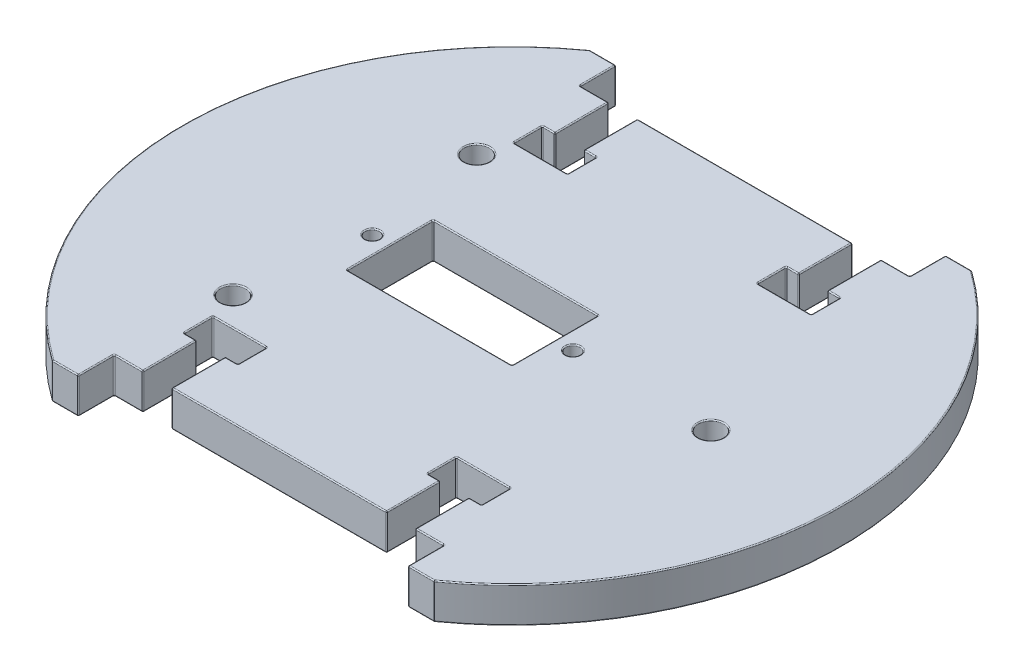
SolidWorks part; units mm, degrees
ref_plane "Front Plane" through (0, 0, 0) normal (0, 0, 1) x (1, 0, 0)
ref_plane "Top Plane" through (0, 0, 0) normal (0, 1, 0) x (1, 0, 0)
ref_plane "Right Plane" through (0, 0, 0) normal (1, 0, 0) x (0, 0, -1)
sketch "Sketch1" plane through (0, 0, 0) normal (0, 1, 0) x (1, 0, 0)
  line L0 (-26.6411, 37.5) -> (-23, 37.5)
  line L1 (0, 0) -> (-46, 0) construction
  line L3 (-23, 37.5) -> (-23, 32.5)
  line L4 (-23, 32.5) -> (23, 32.5)
  line L5 (23, 37.5) -> (23, 32.5)
  line L6 (23, 37.5) -> (26.6411, 37.5)
  line L7 (-26.6411, -37.5) -> (-23, -37.5)
  line L8 (-23, -37.5) -> (-23, -32.5)
  line L9 (-23, -32.5) -> (23, -32.5)
  line L10 (23, -37.5) -> (23, -32.5)
  line L11 (23, -37.5) -> (26.6411, -37.5)
  line L12 (27.75, 0) -> (-21.93, 0) construction
  line L13 (-17, -6) -> (6, -6)
  line L14 (-17, -6) -> (-17, 6)
  line L15 (-17, 6) -> (6, 6)
  line L16 (6, -6) -> (6, 6)
  line L17 (-17, -6) -> (6, 6) construction
  line L18 (-17, 6) -> (6, -6) construction
  line L19 (-21.93, 17) -> (-21.93, -17) construction
  arc A0 (-26.6411, 37.5) -> (-26.6411, -37.5) centre (0, 0) ccw
  arc A1 (26.6411, -37.5) -> (26.6411, 37.5) centre (0, 0) ccw
  circle A2 centre (-19.5, 0) radius 1
  circle A3 centre (8.5, 0) radius 1
  circle A4 centre (-21.93, 17) radius 1.75
  circle A5 centre (-21.93, -17) radius 1.75
  circle A6 centre (27.75, 0) radius 1.75
  point P9 (0, 32.5)
  point P16 (-5.5, 0)
  dimension "D1" = 92
  dimension "D8" = 2
  dimension "D9" = 2
  dimension "D15" = 3.5
  dimension "D2" = 37.5
  dimension "D3" = 46
  dimension "D4" = 5
  dimension "D5" = 6
  dimension "D6" = 23
  dimension "D7" = 12
  dimension "D10" = 2.5
  dimension "D11" = 2.5
  dimension "D12" = 34
  dimension "D13" = 27.75
  dimension "D14" = 49.68
extrude "Boss-Extrude1" add sketch "Sketch1" along normal blind 5
sketch "Sketch2" plane through (0, 5, 0) normal (0, 1, 0) x (1, 0, 0)
  line L0 (23, 32.5) -> (-23, 32.5) construction
  line L1 (-19, 25) -> (-15, 25)
  line L2 (-19, 25) -> (-19, 32.5)
  line L3 (-19, 32.5) -> (-15, 32.5)
  line L4 (-15, 25) -> (-15, 32.5)
  line L5 (-19, 25) -> (-15, 32.5) construction
  line L6 (-19, 32.5) -> (-15, 25) construction
  line L7 (-23, 32.5) -> (-23, 37.5) construction
  line L8 (-20.75, 21) -> (-13.25, 21)
  line L9 (-20.75, 21) -> (-20.75, 25)
  line L10 (-20.75, 25) -> (-13.25, 25)
  line L11 (-13.25, 21) -> (-13.25, 25)
  line L12 (-20.75, 21) -> (-13.25, 25) construction
  line L13 (-20.75, 25) -> (-13.25, 21) construction
  line L14 (-17, 0) -> (0, 0) construction
  line L15 (-17, 6) -> (-17, -6) construction
  line L16 (0, 0) -> (0, 32.5) construction
  line L17 (20.75, 25) -> (13.25, 21) construction
  line L18 (20.75, 21) -> (13.25, 25) construction
  line L19 (19, 32.5) -> (15, 25) construction
  line L20 (19, 25) -> (15, 32.5) construction
  line L21 (13.25, 21) -> (13.25, 25)
  line L22 (20.75, 25) -> (13.25, 25)
  line L23 (20.75, 21) -> (20.75, 25)
  line L24 (20.75, 21) -> (13.25, 21)
  line L25 (15, 25) -> (15, 32.5)
  line L26 (19, 32.5) -> (15, 32.5)
  line L27 (19, 25) -> (19, 32.5)
  line L28 (19, 25) -> (15, 25)
  line L29 (19, -25) -> (15, -32.5) construction
  line L30 (19, -32.5) -> (15, -25) construction
  line L31 (20.75, -21) -> (13.25, -25) construction
  line L32 (20.75, -25) -> (13.25, -21) construction
  line L33 (-20.75, -25) -> (-13.25, -21) construction
  line L34 (-20.75, -21) -> (-13.25, -25) construction
  line L35 (-19, -32.5) -> (-15, -25) construction
  line L36 (-19, -25) -> (-15, -32.5) construction
  line L37 (19, -25) -> (15, -25)
  line L38 (19, -25) -> (19, -32.5)
  line L39 (19, -32.5) -> (15, -32.5)
  line L40 (15, -25) -> (15, -32.5)
  line L41 (20.75, -21) -> (13.25, -21)
  line L42 (20.75, -21) -> (20.75, -25)
  line L43 (20.75, -25) -> (13.25, -25)
  line L44 (13.25, -21) -> (13.25, -25)
  line L45 (-13.25, -21) -> (-13.25, -25)
  line L46 (-20.75, -25) -> (-13.25, -25)
  line L47 (-20.75, -21) -> (-20.75, -25)
  line L48 (-20.75, -21) -> (-13.25, -21)
  line L49 (-15, -25) -> (-15, -32.5)
  line L50 (-19, -32.5) -> (-15, -32.5)
  line L51 (-19, -25) -> (-19, -32.5)
  line L52 (-19, -25) -> (-15, -25)
  point P0 (-17, 28.75)
  point P7 (-17, 23)
  point P28 (17, 23)
  point P29 (17, 28.75)
  point P46 (17, -28.75)
  point P47 (17, -23)
  point P48 (-17, -23)
  point P49 (-17, -28.75)
  dimension "D1" = 4
  dimension "D2" = 4
  dimension "D3" = 7.5
  dimension "D4" = 4
  dimension "D5" = 7.5
extrude "Cut-Extrude1" cut sketch "Sketch2" against normal through all contours L2 L3 L4 L1 | L9 L10 L11 L8 | L25 L26 L27 L28 | L21 L22 L23 L24 | L40 L39 L38 L37 | L44 L43 L42 L41 | L45 L46 L47 L48 | L49 L50 L51 L52
fillet "Fillet1" radius 0.15 123 edges at (-19, 2.5, -25) (-19, 2.5, -32.5) (-15, 2.5, -32.5) (-15, 2.5, -25) (-19, 0, -28.75) (-15, 0, -28.75) (-19, 5, -28.75) (-15, 5, -28.75) (-13.25, 2.5, -25) (-13.25, 2.5, -21) (-20.75, 0, -23) (-19.875, 0, -25) (-14.125, 0, -25) (-17, 0, -21) (-20.75, 5, -23) (-19.875, 5, -25) (-14.125, 5, -25) (-13.25, 5, -23) (-17, 5, -21) (19, 2.5, 25) (19, 2.5, 32.5) (15, 2.5, 25) (19, 0, 28.75) (15, 0, 28.75) (15, 5, 28.75) (20.75, 2.5, 21) (20.75, 0, 23) (19.875, 0, 25) (14.125, 0, 25) (13.25, 0, 23) (20.75, 5, 23) (19.875, 5, 25) (14.125, 5, 25) (13.25, 5, 23) (17, 5, 21) (-13.25, 2.5, 21) (-13.25, 2.5, 25) (-20.75, 2.5, 25) (-20.75, 2.5, 21) (-20.75, 0, 23) (-19.875, 0, 25) (-14.125, 0, 25) (-13.25, 0, 23) (-20.75, 5, 23) (-19.875, 5, 25) (-14.125, 5, 25) (-13.25, 5, 23) (-17, 5, 21) (-15, 2.5, 32.5) (-19, 2.5, 32.5) (-19, 0, 28.75) (-15, 0, 28.75) (-19, 5, 28.75) (13.25, 5, -23) (14.125, 5, -25) (20.75, 5, -23) (17, 0, -21) (13.25, 0, -23) (14.125, 0, -25) (20.75, 0, -23) (20.75, 2.5, -21) (13.25, 2.5, -25) (13.25, 2.5, -21) (15, 5, -28.75) (19, 5, -28.75) (15, 0, -28.75) (19, 2.5, -25) (19, 2.5, -32.5) (15, 2.5, -32.5) (15, 2.5, -25) (-21.93, 0, -15.25) (-21.93, 5, -15.25) (27.75, 5, 1.75) (-21.93, 0, 18.75) (-19.5, 0, 1) (-19.5, 5, 1) (8.5, 0, 1) (8.5, 5, 1) (6, 0, 0) (-5.5, 0, -6) (-17, 0, 0) (6, 5, 0) (-5.5, 5, -6) (-17, 5, 0) (-5.5, 5, 6) (6, 2.5, 6) (-17, 2.5, -6) (-46, 0, 0) (-24.8206, 0, 37.5) (-23, 0, 35) (21, 0, 32.5) (-21, 0, 32.5) (24.8206, 0, 37.5) (46, 0, 0) (24.8206, 0, -37.5) (23, 0, -35) (-21, 0, -32.5) (0, 0, -32.5) (21, 0, -32.5) (-23, 0, -35) (-24.8206, 0, -37.5) (-46, 5, 0) (-24.8206, 5, 37.5) (21, 5, 32.5) (0, 5, 32.5) (23, 5, 35) (24.8206, 5, 37.5) (46, 5, 0) (23, 5, -35) (-21, 5, -32.5) (21, 5, -32.5) (-23, 5, -35) (-26.6411, 2.5, -37.5) (-23, 2.5, -37.5) (-23, 2.5, -32.5) (23, 2.5, -32.5) (23, 2.5, -37.5) (26.6411, 2.5, -37.5) (23, 2.5, 37.5) (23, 2.5, 32.5) (-23, 2.5, 32.5) (-26.6411, 2.5, 37.5) (15, 2.5, 32.5)
